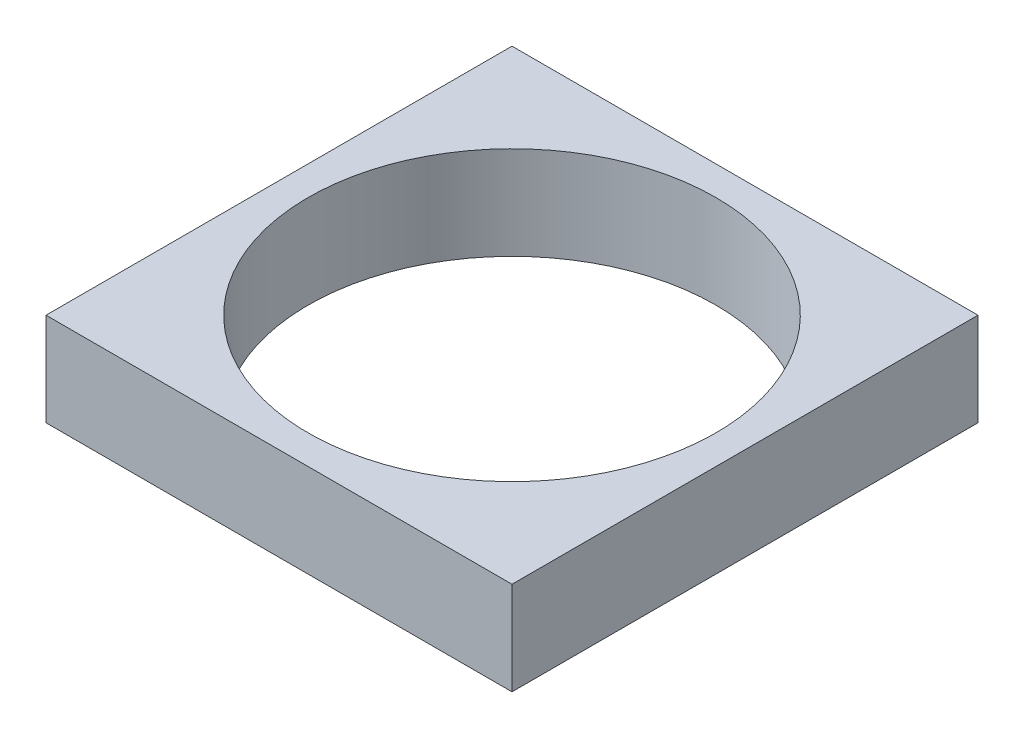
SolidWorks part; units mm, degrees
ref_plane "Front Plane" through (0, 0, 0) normal (0, 0, 1) x (1, 0, 0)
ref_plane "Top Plane" through (0, 0, 0) normal (0, 1, 0) x (1, 0, 0)
ref_plane "Right Plane" through (0, 0, 0) normal (1, 0, 0) x (0, 0, -1)
sketch "Sketch1" plane through (0, 0, 0) normal (0, 1, 0) x (1, 0, 0)
  line L1 (-40, 40) -> (40, 40)
  line L2 (-40, 40) -> (-40, -40)
  line L3 (-40, -40) -> (40, -40)
  line L4 (40, 40) -> (40, -40)
  line L5 (-40, 40) -> (40, -40) construction
  line L6 (-40, -40) -> (40, 40) construction
  point P0 (0, 0)
  dimension "D1" = 80
  dimension "D2" = 80
extrude "Boss-Extrude1" add sketch "Sketch1" along normal blind 16
sketch "Sketch2" plane through (0, 0, 0) normal (0, -1, 0) x (1, 0, 0)
  circle A0 centre (0, 0) radius 35
  dimension "D1" = 70
extrude "Cut-Extrude1" cut sketch "Sketch2" against normal through all
